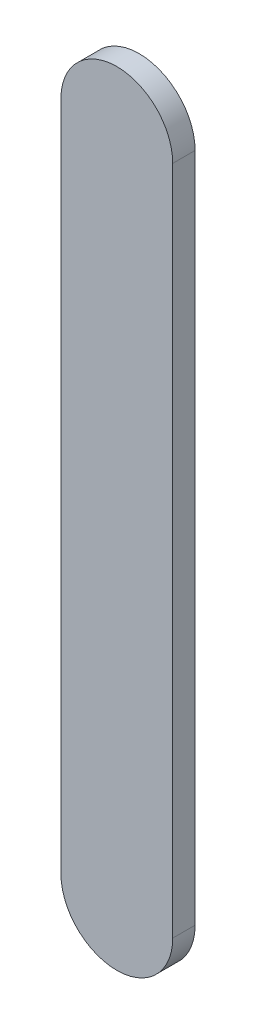
SolidWorks part; units mm, degrees
ref_plane "Front Plane" through (0, 0, 0) normal (0, 0, 1) x (1, 0, 0)
ref_plane "Top Plane" through (0, 0, 0) normal (0, 1, 0) x (1, 0, 0)
ref_plane "Right Plane" through (0, 0, 0) normal (1, 0, 0) x (0, 0, -1)
sketch "Sketch1" plane through (0, 0, 0) normal (0, 0, 1) x (1, 0, 0)
  line L0 (6.7838, 6.5795) -> (6.7838, -23.4205) construction
  line L1 (9.2838, 6.5795) -> (9.2838, -23.4205)
  line L2 (4.2838, 6.5795) -> (4.2838, -23.4205)
  arc A0 (9.2838, 6.5795) -> (4.2838, 6.5795) centre (6.7838, 6.5795) ccw
  arc A1 (4.2838, -23.4205) -> (9.2838, -23.4205) centre (6.7838, -23.4205) ccw
  point P2 (6.7838, -8.4205)
  dimension "D1" = 30
extrude "Boss-Extrude1" add sketch "Sketch1" along normal blind 1
